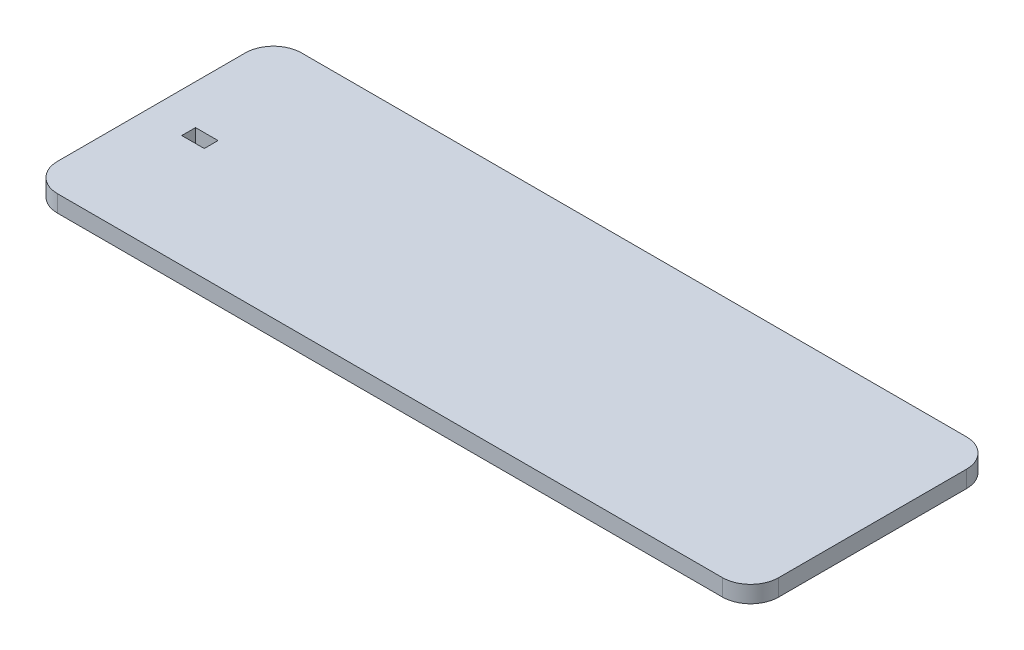
SolidWorks part; units mm, degrees
ref_plane "Front Plane" through (0, 0, 0) normal (0, 0, 1) x (1, 0, 0)
ref_plane "Top Plane" through (0, 0, 0) normal (0, 1, 0) x (1, 0, 0)
ref_plane "Right Plane" through (0, 0, 0) normal (1, 0, 0) x (0, 0, -1)
sketch "Sketch2" plane through (0, 0, 0) normal (0, 1, 0) x (1, 0, 0)
  line L1 (-221.1991, 35.0362) -> (35.2484, 35.0362)
  line L2 (-221.1991, 35.0362) -> (-221.1991, 121.8)
  line L3 (-221.1991, 121.8) -> (35.2484, 121.8)
  line L4 (35.2484, 35.0362) -> (35.2484, 121.8)
  line L5 (-221.1991, 35.0362) -> (35.2484, 121.8) construction
  line L6 (-221.1991, 121.8) -> (35.2484, 35.0362) construction
  point P0 (-92.9754, 78.4181)
extrude "Boss-Extrude2" add sketch "Sketch2" along normal blind 6
sketch "Sketch5" plane through (0, 0, 0) normal (0, -1, 0) x (1, 0, 0)
  line L1 (-207.05, -79.95) -> (-199.05, -79.95)
  line L2 (-207.05, -79.95) -> (-207.05, -75.05)
  line L3 (-207.05, -75.05) -> (-199.05, -75.05)
  line L4 (-199.05, -79.95) -> (-199.05, -75.05)
  line L5 (-207.05, -79.95) -> (-199.05, -75.05) construction
  line L6 (-207.05, -75.05) -> (-199.05, -79.95) construction
  point P0 (-203.05, -77.5)
  dimension "D2" = 8
extrude "Cut-Extrude7" cut sketch "Sketch5" against normal through all both and the other way through all
fillet "Fillet1" radius 10 4 edges at (-221.1991, 3, -121.8) (35.2484, 3, -121.8) (35.2484, 3, -35.0362) (-221.1991, 3, -35.0362)
